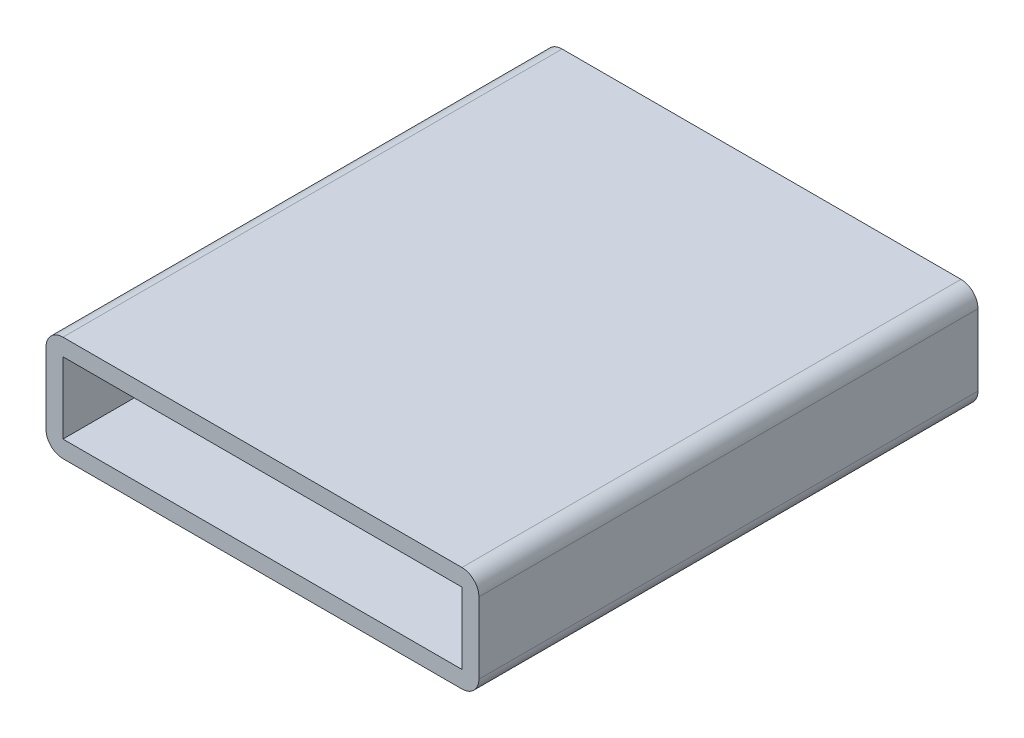
SolidWorks part; units mm, degrees
ref_plane "Front Plane" through (0, 0, 0) normal (0, 0, 1) x (1, 0, 0)
ref_plane "Top Plane" through (0, 0, 0) normal (0, 1, 0) x (1, 0, 0)
ref_plane "Right Plane" through (0, 0, 0) normal (1, 0, 0) x (0, 0, -1)
sketch "Sketch1" plane through (0, 0, 0) normal (0, 0, 1) x (1, 0, 0)
  line L1 (-16.1925, 3.937) -> (16.1925, 3.937)
  line L2 (-16.1925, 3.937) -> (-16.1925, -3.937)
  line L3 (-16.1925, -3.937) -> (16.1925, -3.937)
  line L4 (16.1925, 3.937) -> (16.1925, -3.937)
  line L5 (-16.1925, 3.937) -> (16.1925, -3.937) construction
  line L6 (-16.1925, -3.937) -> (16.1925, 3.937) construction
  line L7 (-14.9225, 2.667) -> (14.9225, 2.667)
  line L8 (-14.9225, 2.667) -> (-14.9225, -2.667)
  line L9 (-14.9225, -2.667) -> (14.9225, -2.667)
  line L10 (14.9225, 2.667) -> (14.9225, -2.667)
  line L11 (-14.9225, 2.667) -> (14.9225, -2.667) construction
  line L12 (-14.9225, -2.667) -> (14.9225, 2.667) construction
  point P0 (0, 0)
  point P6 (0, 0)
  dimension "D1" = 29.845
  dimension "D2" = 5.334
  dimension "D3" = 1.27
  dimension "D4" = 1.27
extrude "Boss-Extrude1" add sketch "Sketch1" against normal blind 37.338
fillet "Fillet1" radius 1.27 4 edges at (16.1925, -3.937, -18.669) (-16.1925, -3.937, -18.669) (16.1925, 3.937, -18.669) (-16.1925, 3.937, -18.669)
sketch "Sketch2" plane through (0, 0, -37.338) normal (0, 0, -1) x (-1, 0, 0)
  line L1 (-14.9225, 2.667) -> (14.9225, 2.667)
  line L2 (-14.9225, 2.667) -> (-14.9225, -2.667)
  line L3 (-14.9225, -2.667) -> (14.9225, -2.667)
  line L4 (14.9225, 2.667) -> (14.9225, -2.667)
  line L5 (-14.9225, 2.667) -> (14.9225, -2.667) construction
  line L6 (-14.9225, -2.667) -> (14.9225, 2.667) construction
  line L7 (-2.794, 2.54) -> (2.794, 2.54)
  line L8 (-3.81, 1.524) -> (-3.81, -1.524)
  line L9 (-2.794, -2.54) -> (2.794, -2.54)
  line L10 (3.81, 1.524) -> (3.81, -1.524)
  line L11 (-3.81, 2.54) -> (3.81, -2.54) construction
  line L12 (-3.81, -2.54) -> (3.81, 2.54) construction
  arc A0 (2.794, 2.54) -> (3.81, 1.524) centre (2.794, 1.524) cw
  arc A1 (-3.81, -1.524) -> (-2.794, -2.54) centre (-2.794, -1.524) ccw
  arc A2 (2.794, -2.54) -> (3.81, -1.524) centre (2.794, -1.524) ccw
  arc A3 (-2.794, 2.54) -> (-3.81, 1.524) centre (-2.794, 1.524) ccw
  point P0 (0, 0)
  point P7 (0, 0)
  dimension "D3" = 1.016
  dimension "D1" = 7.62
  dimension "D2" = 5.08
extrude "Boss-Extrude2" add sketch "Sketch2" against normal blind 1.27
